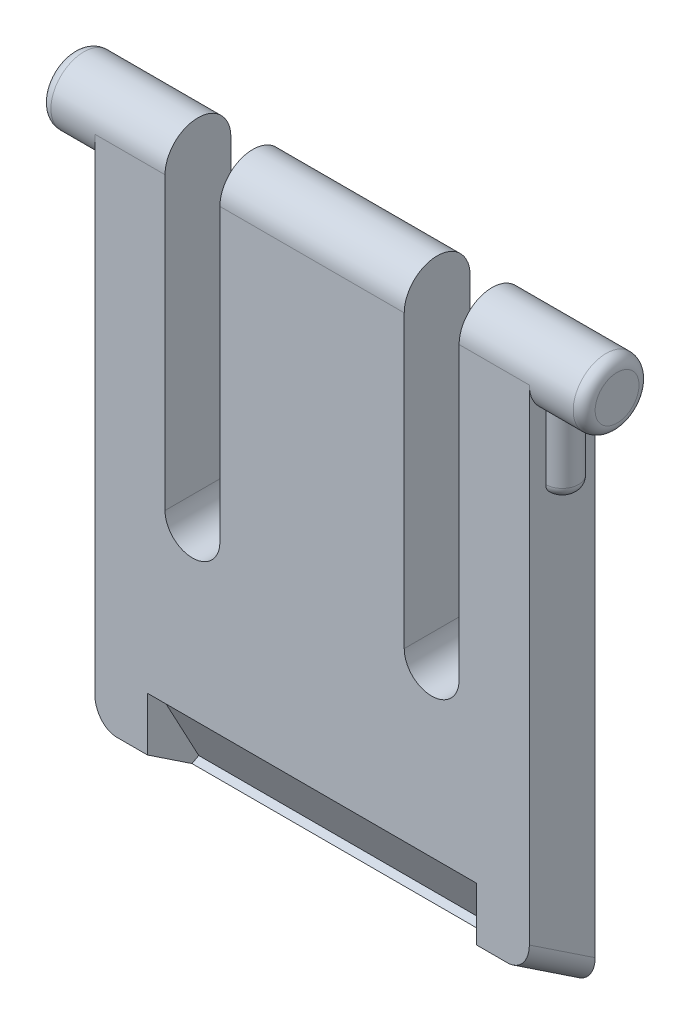
SolidWorks part; units mm, degrees
ref_plane "Front" through (0, 0, 0) normal (0, 0, 1) x (1, 0, 0)
ref_plane "Top" through (0, 0, 0) normal (0, 1, 0) x (1, 0, 0)
ref_plane "Right" through (0, 0, 0) normal (1, 0, 0) x (0, 0, -1)
sketch "Sketch1" plane through (0, 0, 0) normal (0, 0, 1) x (1, 0, 0)
  line L0 (3.2, 25.3) -> (3.2, 12.05)
  line L1 (0, 0) -> (19.8, 0)
  line L2 (0, 0) -> (0, 25.3)
  line L3 (0, 25.3) -> (3.2, 25.3)
  line L4 (19.8, 0) -> (19.8, 25.3)
  line L5 (5.7, 25.3) -> (5.7, 12.05)
  line L6 (9.9, 26.8) -> (9.9, 0) construction
  line L7 (14.1, 25.3) -> (14.1, 12.05)
  line L8 (16.6, 25.3) -> (16.6, 12.05)
  line L9 (16.6, 25.3) -> (19.8, 25.3)
  line L10 (5.7, 25.3) -> (14.1, 25.3)
  arc A0 (3.2, 12.05) -> (5.7, 12.05) centre (4.45, 12.05) ccw
  arc A1 (16.6, 12.05) -> (14.1, 12.05) centre (15.35, 12.05) cw
  point P13 (5.7, 12.1237)
  dimension "D5" = 14.5
  dimension "D1" = 19.8
  dimension "D2" = 25.3
  dimension "D3" = 3.2
  dimension "D4" = 2.5
extrude "Boss-Extrude1" add sketch "Sketch1" along normal blind 3
sketch "Sketch2" plane through (19.8, 0, 0) normal (1, 0, 0) x (0, 0, -1)
  line L0 (-3, 25.3) -> (0, 25.3) construction
  circle A0 centre (-1.5, 25.3) radius 1.5
extrude "Boss-Extrude2" add sketch "Sketch2" against normal blind 22.3 and the other way blind 2.5 contours A0
sketch "Sketch3" plane through (0, 0, 0) normal (0, 0, 1) x (1, 0, 0)
  line L0 (5.7, 25.3) -> (5.7, 12.05) construction
  line L1 (3.2, 12.05) -> (5.7, 12.05)
  line L2 (3.2, 12.05) -> (3.2, 32.7838)
  line L3 (3.2, 32.7838) -> (5.7, 32.7838)
  line L4 (5.7, 12.05) -> (5.7, 32.7838)
  line L5 (14.1, 12.05) -> (16.6, 12.05)
  line L6 (14.1, 12.05) -> (14.1, 32.7838)
  line L7 (14.1, 32.7838) -> (16.6, 32.7838)
  line L8 (16.6, 12.05) -> (16.6, 32.7838)
  point P10 (16.6, 13.55)
  point P12 (5.7, 13.55)
  dimension "D1" = 20.7338
extrude "Cut-Extrude1" cut sketch "Sketch3" against normal through all and the other way through all
ref_plane "Plane1" through (0, 26.8, 0) normal (0, 1, 0) x (1, 0, 0)
sketch "Sketch5" plane through (0, 26.8, 0) normal (0, 1, 0) x (1, 0, 0)
  line L0 (0, 0) -> (0, -3) construction
  line L1 (0, -0.75) -> (0, -2.25)
  arc A0 (0, -0.75) -> (0, -2.25) centre (0, -1.5) ccw
  dimension "D1" = 1.5
extrude "Boss-Extrude3" add sketch "Sketch5" against normal blind 5.8 from offset 0.5 offset against normal yes
fillet "Fillet1" radius 0.5 1 edges at (-0.75, 20.5, 1.5)
ref_plane "Plane2" through (9.9, 0, 0) normal (-1, 0, 0) x (0, 0, 1)
mirror "Mirror1" about plane through (9.9, 0, 0) normal (-1, 0, 0) of "Fillet1", "Boss-Extrude3"
sketch "Sketch6" plane through (0, 0, 0) normal (-1, 0, 0) x (0, 0, 1)
  line L0 (0, 26.8) -> (0, 0) construction
  line L1 (0, 0) -> (3, 2)
  line L2 (3, 25.3) -> (3, 0) construction
  line L3 (3, 2) -> (3, 26.8) construction
  line L4 (3, 26.8) -> (0, 26.8) construction
  line L5 (0, 0) -> (0, -2.5922)
  line L6 (0, -2.5922) -> (3, -2.5922)
  line L7 (3, -2.5922) -> (3, 2)
  circle A0 centre (1.5, 25.3) radius 1.5 construction
  dimension "D1" = 24.8
extrude "Cut-Extrude2" cut sketch "Sketch6" against normal through all
sketch "Sketch7" plane through (0, 0, 0) normal (-1, 0, 0) x (0, 0, 1)
  line L0 (3, 2) -> (-3.2434, 5.3414)
  line L1 (3, 2) -> (0, 0) construction
  line L2 (3, 25.3) -> (3, 2) construction
  dimension "D1" = 123.69
  dimension "D2" = 61.845
ref_plane "Plane3" through (0, -0.8028, 1.5) normal (0, 0.4719, -0.8817) x (-1, 0, 0)
sketch "Sketch8" plane through (0, -0.8028, 1.5) normal (0, 0.4719, -0.8817) x (-1, 0, 0)
  line L0 (-19.8, 3.1789) -> (0, 3.1789) construction
  line L1 (-2.4, 5.3289) -> (-17.4, 5.3289)
  line L2 (-2.4, 5.3289) -> (-2.4, 1.0289)
  line L3 (-2.4, 1.0289) -> (-17.4, 1.0289)
  line L4 (-17.4, 5.3289) -> (-17.4, 1.0289)
  line L5 (-2.4, 5.3289) -> (-17.4, 1.0289) construction
  line L6 (-2.4, 1.0289) -> (-17.4, 5.3289) construction
  point P0 (-9.9, 3.1789)
  point P7 (-16.5618, 1.1876)
  point P8 (0, 0)
  dimension "D1" = 4.3
  dimension "D2" = 15
extrude "Cut-Extrude3" cut sketch "Sketch8" along normal blind 1.5
fillet "Fillet2" radius 0.5 2 edges at (-2.5, 25.3, 0) (22.3, 25.3, 0)
fillet "Fillet3" radius 1 2 edges at (19.8, 1, 1.5) (0, 1, 1.5)
